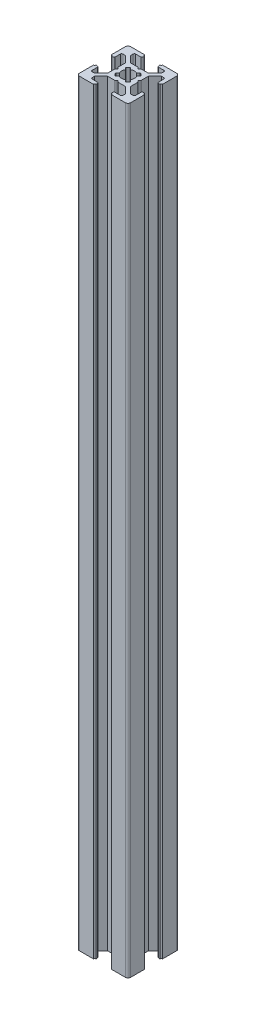
SolidWorks part; units mm, degrees
ref_plane "Front Plane" through (0, 0, 0) normal (0, 0, 1) x (1, 0, 0)
ref_plane "Top Plane" through (0, 0, 0) normal (0, 1, 0) x (1, 0, 0)
ref_plane "Right Plane" through (0, 0, 0) normal (1, 0, 0) x (0, 0, -1)
sketch "Sketch3" plane through (0, 0, 0) normal (0, 1, 0) x (1, 0, 0)
  line L0 (7, 20) -> (7, 18.5)
  line L1 (0, 0) -> (20, 0)
  line L2 (0, 0) -> (0, 20)
  line L3 (0, 20) -> (20, 20)
  line L4 (20, 0) -> (20, 20)
  line L5 (7, 18.5) -> (4, 18.5)
  line L6 (4, 18.5) -> (4, 17)
  line L7 (4, 17) -> (6.5, 14.5)
  line L8 (6.5, 14.5) -> (13.5, 14.5)
  line L9 (13.5, 14.5) -> (16, 17)
  line L10 (16, 17) -> (16, 18.5)
  line L11 (16, 18.5) -> (13, 18.5)
  line L12 (13, 18.5) -> (13, 20)
  line L13 (13, 20) -> (7, 20)
  line L14 (9.5, 14.5) -> (10, 14)
  line L15 (10, 14) -> (10.5, 14.5)
  line L16 (10.5, 14.5) -> (9.5, 14.5)
  line L17 (13, 19.5) -> (13, 20)
  line L18 (13.5, 20) -> (13, 20)
  line L19 (7, 19.5) -> (7, 20)
  line L20 (6.5, 20) -> (7, 20)
  line L21 (0, 13) -> (1.5, 13)
  line L22 (1.5, 13) -> (1.5, 16)
  line L23 (1.5, 16) -> (3, 16)
  line L24 (3, 16) -> (5.5, 13.5)
  line L25 (5.5, 13.5) -> (5.5, 6.5)
  line L26 (5.5, 6.5) -> (3, 4)
  line L27 (3, 4) -> (1.5, 4)
  line L28 (1.5, 4) -> (1.5, 7)
  line L29 (1.5, 7) -> (0, 7)
  line L30 (0, 7) -> (0, 13)
  line L31 (5.5, 10.5) -> (5.5, 9.5)
  line L32 (5.5, 9.5) -> (6, 10)
  line L33 (6, 10) -> (5.5, 10.5)
  line L34 (0.5, 13) -> (0, 13)
  line L35 (0, 13.5) -> (0, 13)
  line L36 (0, 6.5) -> (0, 7)
  line L37 (0.5, 7) -> (0, 7)
  line L38 (10, 20) -> (10, 0) construction
  line L39 (20, 10) -> (0, 10) construction
  line L40 (10, 6) -> (10.5, 5.5)
  line L41 (9.5, 5.5) -> (10, 6)
  line L42 (10.5, 5.5) -> (9.5, 5.5)
  line L43 (13.5, 0) -> (13, 0)
  line L44 (13, 0.5) -> (13, 0)
  line L45 (6.5, 0) -> (7, 0)
  line L46 (7, 0.5) -> (7, 0)
  line L47 (13, 1.5) -> (13, 0)
  line L48 (16, 1.5) -> (13, 1.5)
  line L49 (16, 3) -> (16, 1.5)
  line L50 (13.5, 5.5) -> (16, 3)
  line L51 (6.5, 5.5) -> (13.5, 5.5)
  line L52 (4, 3) -> (6.5, 5.5)
  line L53 (4, 1.5) -> (4, 3)
  line L54 (7, 1.5) -> (4, 1.5)
  line L55 (7, 0) -> (7, 1.5)
  line L56 (13, 0) -> (7, 0)
  line L57 (14.5, 9.5) -> (14, 10)
  line L58 (14.5, 10.5) -> (14.5, 9.5)
  line L59 (14, 10) -> (14.5, 10.5)
  line L60 (19.5, 7) -> (20, 7)
  line L61 (20, 6.5) -> (20, 7)
  line L62 (20, 13.5) -> (20, 13)
  line L63 (19.5, 13) -> (20, 13)
  line L64 (18.5, 7) -> (20, 7)
  line L65 (18.5, 4) -> (18.5, 7)
  line L66 (17, 4) -> (18.5, 4)
  line L67 (14.5, 6.5) -> (17, 4)
  line L68 (14.5, 13.5) -> (14.5, 6.5)
  line L69 (17, 16) -> (14.5, 13.5)
  line L70 (18.5, 16) -> (17, 16)
  line L71 (18.5, 13) -> (18.5, 16)
  line L72 (20, 13) -> (18.5, 13)
  line L73 (20, 7) -> (20, 13)
  arc A0 (13.5, 20) -> (13, 19.5) centre (13, 20) cw
  arc A1 (6.5, 20) -> (7, 19.5) centre (7, 20) ccw
  arc A2 (0.5, 13) -> (0, 13.5) centre (0, 13) ccw
  arc A3 (0.5, 7) -> (0, 6.5) centre (0, 7) cw
  arc A4 (13.5, 0) -> (13, 0.5) centre (13, 0) ccw
  arc A5 (6.5, 0) -> (7, 0.5) centre (7, 0) cw
  arc A6 (19.5, 7) -> (20, 6.5) centre (20, 7) ccw
  arc A7 (19.5, 13) -> (20, 13.5) centre (20, 13) cw
  point P7 (10, 14.5)
  point P16 (10, 20)
  point P26 (5.5, 10)
  point P35 (0, 10)
  dimension "D16" = 0.5
  dimension "D17" = 0.5
  dimension "D28" = 0.5
  dimension "D29" = 0.5
  dimension "D1" = 20
  dimension "D2" = 20
  dimension "D3" = 7
  dimension "D4" = 7
  dimension "D5" = 1.5
  dimension "D6" = 1.5
  dimension "D7" = 3
  dimension "D8" = 3
  dimension "D9" = 1.5
  dimension "D10" = 1.5
  dimension "D11" = 7
  dimension "D12" = 5.5
  dimension "D13" = 0.5
  dimension "D14" = 0.5
  dimension "D15" = 0.5
  dimension "D18" = 7
  dimension "D19" = 7
  dimension "D20" = 1.5
  dimension "D21" = 1.5
  dimension "D22" = 3
  dimension "D23" = 7
  dimension "D24" = 5.5
  dimension "D25" = 0.5
  dimension "D26" = 0.5
  dimension "D27" = 0.5
extrude "Boss-Extrude1" add sketch "Sketch3" along normal blind 296 contours L72 A7 L4 L3 A0 L12 L11 L10 L9 L8 L15 L14 L7 L6 L5 L0 A1 L2 A2 L21 L22 L23 L24 L25 L33 L32 L26 L27 L28 L29 A3 L1 A5 L55 L54 L53 L52 L51 L41 L40 L50 L49 L48 L47 A4
fillet "Fillet1" radius 1 4 edges at (0, 148, 0) (20, 148, 0) (20, 148, -20) (0, 148, -20)
sketch "Sketch4" plane through (0, 296, 0) normal (0, 1, 0) x (1, 0, 0)
  line L0 (13.5, 14.5) -> (5.5, 6.5) construction
  line L1 (14.5, 13.5) -> (6.5, 5.5) construction
  line L2 (10.5, 14.5) -> (14.5, 10.5) construction
  line L3 (12, 13) -> (13, 12)
  line L4 (13, 12) -> (8, 7)
  line L5 (8, 7) -> (7, 8)
  line L6 (7, 8) -> (12, 13)
  line L7 (13.5, 14.5) -> (16, 17) construction
  line L8 (17, 16) -> (14.5, 13.5) construction
  line L9 (5.5, 9.5) -> (9.5, 5.5) construction
  line L10 (5.5, 10.5) -> (9.5, 14.5) construction
  line L11 (14.5, 9.5) -> (10.5, 5.5) construction
  line L12 (6.5, 14.5) -> (14.5, 6.5) construction
  line L13 (5.5, 13.5) -> (13.5, 5.5) construction
  line L14 (7, 12) -> (8, 13)
  line L15 (8, 13) -> (13, 8)
  line L16 (13, 8) -> (12, 7)
  line L17 (12, 7) -> (7, 12)
  line L18 (4, 17) -> (6.5, 14.5) construction
  line L19 (3, 16) -> (5.5, 13.5) construction
  line L20 (20, 10) -> (0, 10) construction
  circle A0 centre (10, 10) radius 2.5
  dimension "D1" = 5
extrude "Cut-Extrude1" cut sketch "Sketch4" against normal through all contours L6 A0 L15 | L4 A0 L6 L15 | L15 A0 L17 L6 | L17 L4 L15 L6 | L17 A0 L6 | L6 A0 L4 L17 | L4 A0 L17 | L17 A0 L15 L4 | L15 A0 L4 | A0 L6 L5 L4 | A0 L17 L16 L15 | A0 L4 L3 L6 | A0 L15 L14 L17
fillet "Fillet2" radius 0.5 24 edges at (1.5, 148, -16) (1.5, 148, -13) (5.5, 148, -10.5) (5.5, 148, -9.5) (1.5, 148, -7) (1.5, 148, -4) (4, 148, -1.5) (7, 148, -1.5) (9.5, 148, -5.5) (10.5, 148, -5.5) (13, 148, -1.5) (16, 148, -1.5) (18.5, 148, -4) (18.5, 148, -7) (18.5, 148, -13) (18.5, 148, -16) (14.5, 148, -9.5) (14.5, 148, -10.5) (10.5, 148, -14.5) (9.5, 148, -14.5) (16, 148, -18.5) (13, 148, -18.5) (7, 148, -18.5) (4, 148, -18.5)
fillet "Fillet3" radius 0.25 8 edges at (13, 148, -8) (12, 148, -7) (13, 148, -12) (12, 148, -13) (8, 148, -13) (7, 148, -12) (7, 148, -8) (8, 148, -7)
